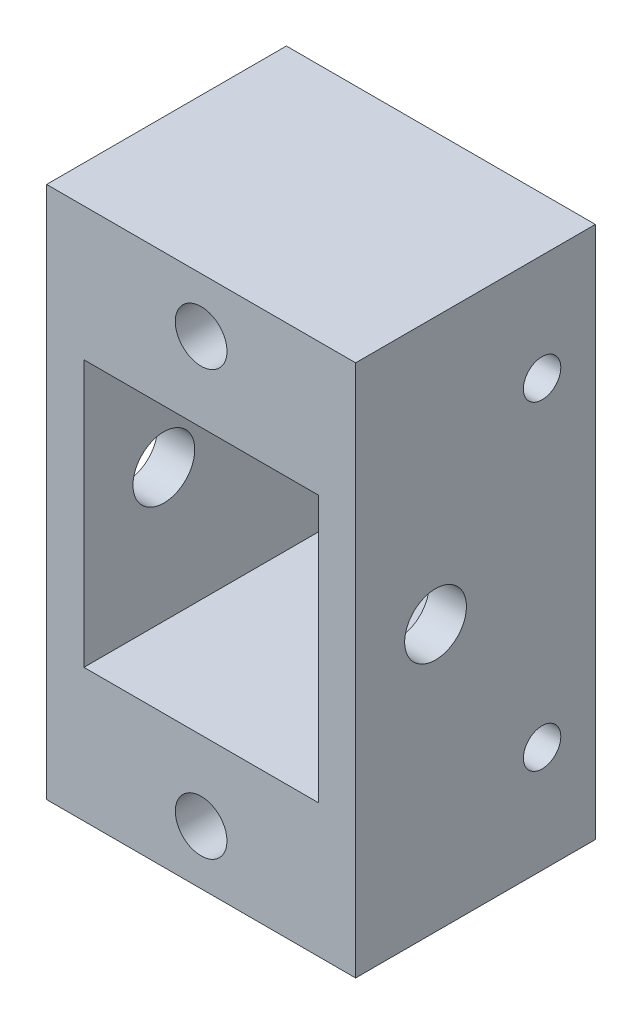
SolidWorks part; units mm, degrees
ref_plane "Front Plane" through (0, 0, 0) normal (0, 0, 1) x (1, 0, 0)
ref_plane "Top Plane" through (0, 0, 0) normal (0, 1, 0) x (1, 0, 0)
ref_plane "Right Plane" through (0, 0, 0) normal (1, 0, 0) x (0, 0, -1)
sketch "Sketch2" plane through (0, 0, 0) normal (0, 0, 1) x (1, 0, 0)
  line L0 (-11, 0) -> (11, 0) construction
  line L1 (-14.5, 25) -> (14.5, 25)
  line L2 (-14.5, 25) -> (-14.5, -25)
  line L3 (-14.5, -25) -> (14.5, -25)
  line L4 (14.5, 25) -> (14.5, -25)
  line L5 (-11, 12.5) -> (11, 12.5)
  line L6 (-11, 12.5) -> (-11, -12.5)
  line L7 (-11, -12.5) -> (11, -12.5)
  line L8 (11, 12.5) -> (11, -12.5)
  circle A0 centre (0, 19.9) radius 2.425
  circle A1 centre (0, -19.9) radius 2.425
  point P4 (0, 25)
  point P6 (-14.5, 0)
  point P11 (0, 12.5)
  point P12 (11, 0)
  dimension "D5" = 4.85
  dimension "D1" = 29
  dimension "D2" = 50
  dimension "D3" = 22
  dimension "D4" = 25
  dimension "D6" = 19.9
extrude "Boss-Extrude1" add sketch "Sketch2" along normal blind 22.5
sketch "Sketch3" plane through (14.5, 0, 0) normal (1, 0, 0) x (0, 0, -1)
  line L0 (-22.5, 25) -> (0, 25) construction
  line L1 (-5, 15) -> (-5, -15) construction
  line L2 (0, -25) -> (0, 25) construction
  circle A1 centre (-5, 15) radius 1.755
  circle A2 centre (-5, -15) radius 1.755
  circle A3 centre (-15, 0) radius 2.9
  point P4 (-11.25, 25)
  point P12 (0, 0)
  point P13 (0, 0)
  point P14 (-10.2006, 25.3274)
  point P15 (0, 0)
  point P16 (-5, 0)
  dimension "D1" = 5.8
  dimension "D2" = 3.51
  dimension "D3" = 30
  dimension "D4" = 15
  dimension "D5" = 25
  dimension "D6" = 10
extrude "Cut-Extrude1" cut sketch "Sketch3" against normal blind 30
